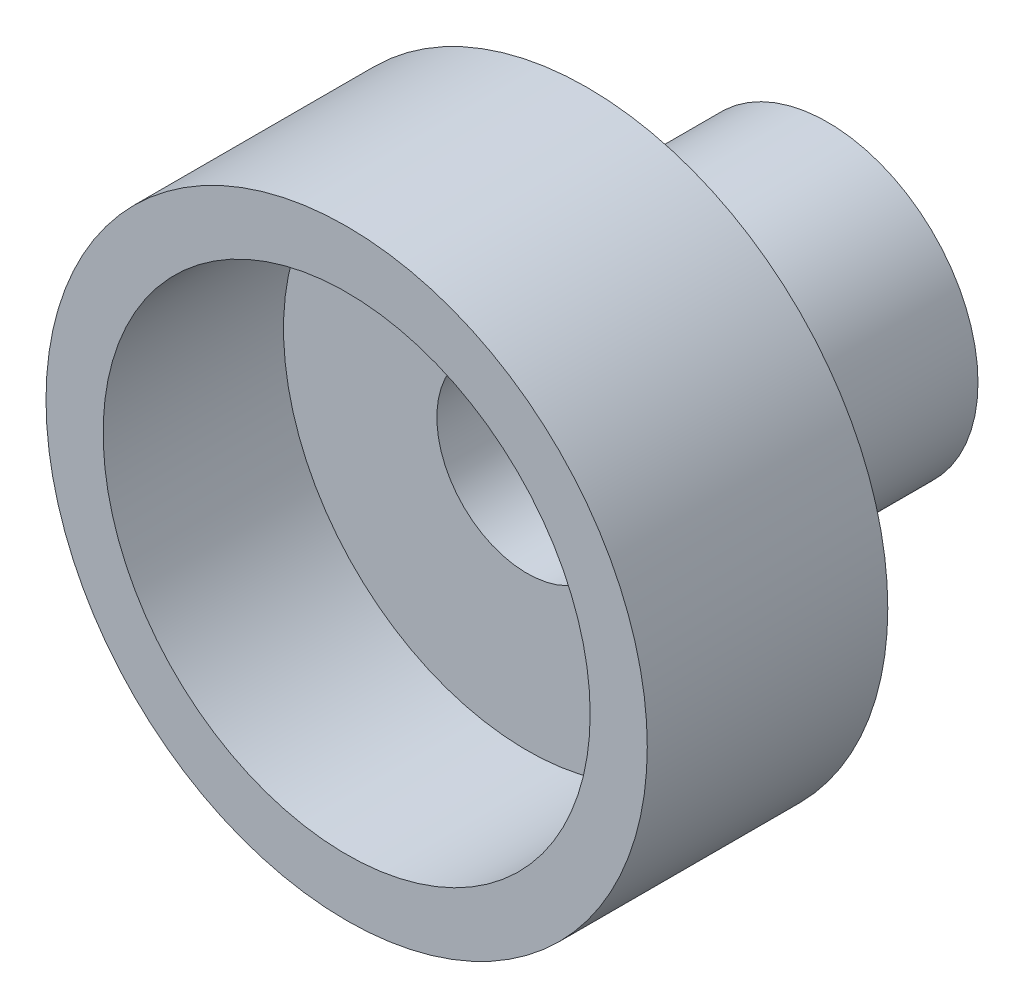
SolidWorks part; units mm, degrees
ref_plane "前视基准面" through (0, 0, 0) normal (0, 0, 1) x (1, 0, 0)
ref_plane "上视基准面" through (0, 0, 0) normal (0, 1, 0) x (1, 0, 0)
ref_plane "右视基准面" through (0, 0, 0) normal (1, 0, 0) x (0, 0, -1)
sketch "草图1" plane through (0, 0, 0) normal (0, 0, 1) x (1, 0, 0)
  circle A0 centre (0, 0) radius 5
extrude "凸台-拉伸1" add sketch "草图1" along normal blind 4
sketch "草图4" plane through (0, 0, 0) normal (0, 0, -1) x (-1, 0, 0)
  circle A0 centre (0, 0) radius 2.5
extrude "凸台-拉伸2" add sketch "草图4" along normal blind 4
sketch "草图2" plane through (0, 0, 0) normal (0, 0, -1) x (-1, 0, 0)
  circle A0 centre (0, 0) radius 1.5
extrude "切除-拉伸1" cut sketch "草图2" along direction (0, 0, -1) on the side against the normal blind 3 and the other way up to surface (4 mm away)
sketch "草图3" plane through (0, 0, 4) normal (0, 0, 1) x (1, 0, 0)
  circle A0 centre (0, 0) radius 4.05
extrude "切除-拉伸2" cut sketch "草图3" against normal blind 3
